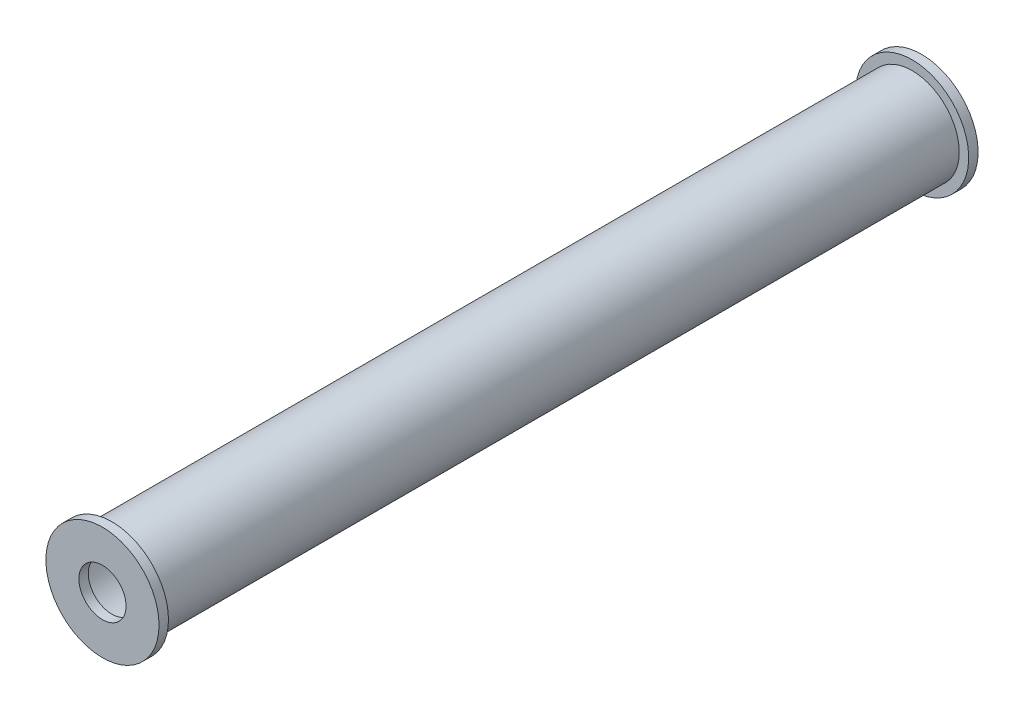
SolidWorks part; units mm, degrees
material "Plain Carbon Steel"
ref_plane "Спереди" through (0, 0, 0) normal (0, 0, 1) x (1, 0, 0)
ref_plane "Сверху" through (0, 0, 0) normal (0, 1, 0) x (1, 0, 0)
ref_plane "Справа" through (0, 0, 0) normal (1, 0, 0) x (0, 0, -1)
other "Configuration Table"
sketch "Sketch1" plane through (0, 0, 0) normal (0, 0, 1) x (1, 0, 0)
  circle A0 centre (0, 0) radius 5
  circle A1 centre (0, 0) radius 4.5
  dimension "D1" = 10
  dimension "D2" = 0.5
extrude "Boss-Extrude1" add sketch "Sketch1" along normal blind 84.88
sketch "Sketch2" plane through (0, 0, 0) normal (0, 0, -1) x (-1, 0, 0)
  circle A0 centre (0, 0) radius 6
  circle A1 centre (0, 0) radius 2.5
  dimension "D1" = 5
  dimension "D2" = 12
extrude "Boss-Extrude2" add sketch "Sketch2" along normal blind 1
sketch "Sketch3" plane through (0, 0, 84.88) normal (0, 0, 1) x (1, 0, 0)
  circle A0 centre (0, 0) radius 6
  circle A1 centre (0, 0) radius 2.5
extrude "Boss-Extrude3" add sketch "Sketch3" along normal blind 1
